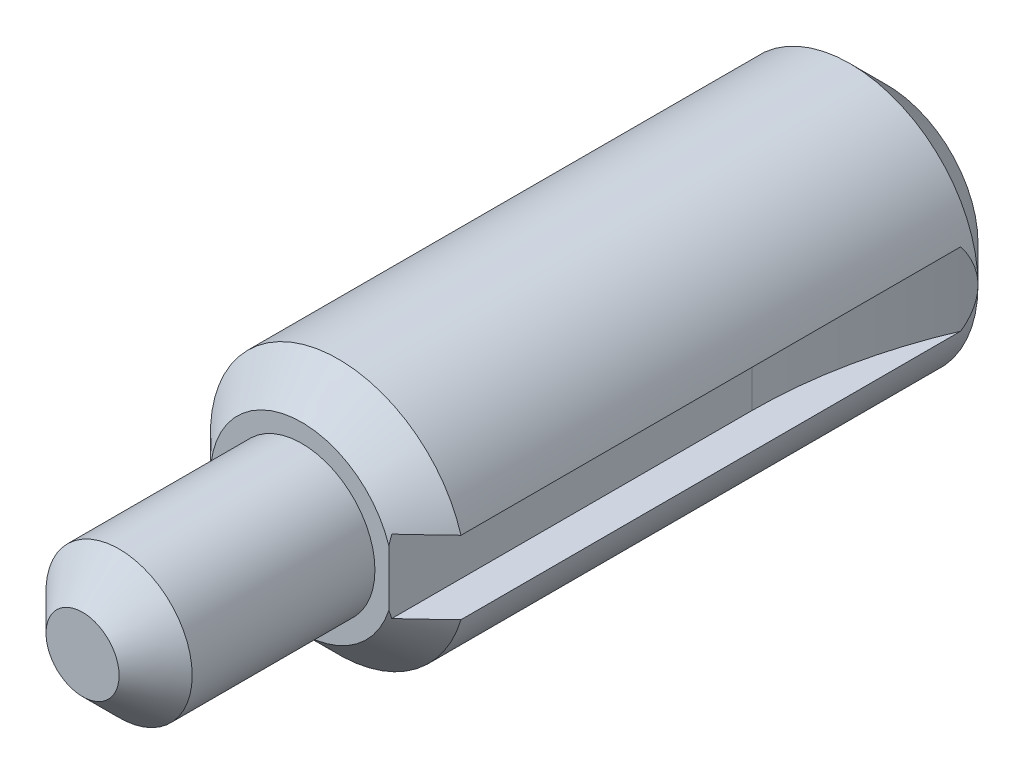
SolidWorks part; units mm, degrees
ref_plane "Front" through (0, 0, 0) normal (0, 0, 1) x (1, 0, 0)
ref_plane "Top" through (0, 0, 0) normal (0, 1, 0) x (1, 0, 0)
ref_plane "Right" through (0, 0, 0) normal (1, 0, 0) x (0, 0, -1)
sketch "Sketch1" plane through (0, 0, 0) normal (0, 0, 1) x (1, 0, 0)
  circle A0 centre (0, 0) radius 5.5562
  dimension "D1" = 11.1125
extrude "Extrude1" add sketch "Sketch1" along normal blind 25.4
sketch "Sketch2" plane through (0, 0, 25.4) normal (0, 0, 1) x (1, 0, 0)
  circle A0 centre (0, 0) radius 3.175
  dimension "D1" = 6.35
extrude "Extrude2" add sketch "Sketch2" along normal blind 9.525
chamfer "Chamfer1" distance 1.5875 3 edges at (3.175, 0, 34.925) (5.5562, 0, 25.4) (5.5562, 0, 0)
sketch "Sketch3" plane through (0, 0, 0) normal (0, 1, 0) x (1, 0, 0)
  line L1 (3.7783, -9.6237) -> (3.7783, -25.4)
  line L2 (-5.5562, -25.4) -> (5.5562, -25.4) construction
  line L3 (5.5562, -1.5875) -> (5.5563, -25.4)
  line L4 (5.5563, -25.4) -> (3.7783, -25.4)
  line L5 (-3.175, -25.4) -> (3.175, -25.4) construction
  arc A0 (5.5562, -1.5875) -> (3.7783, -9.6237) centre (22.8283, -9.6237) ccw
  dimension "D2" = 19.05
  dimension "D1" = 1.778
extrude "Cut-Extrude1" cut sketch "Sketch3" against normal mid plane 3.175
